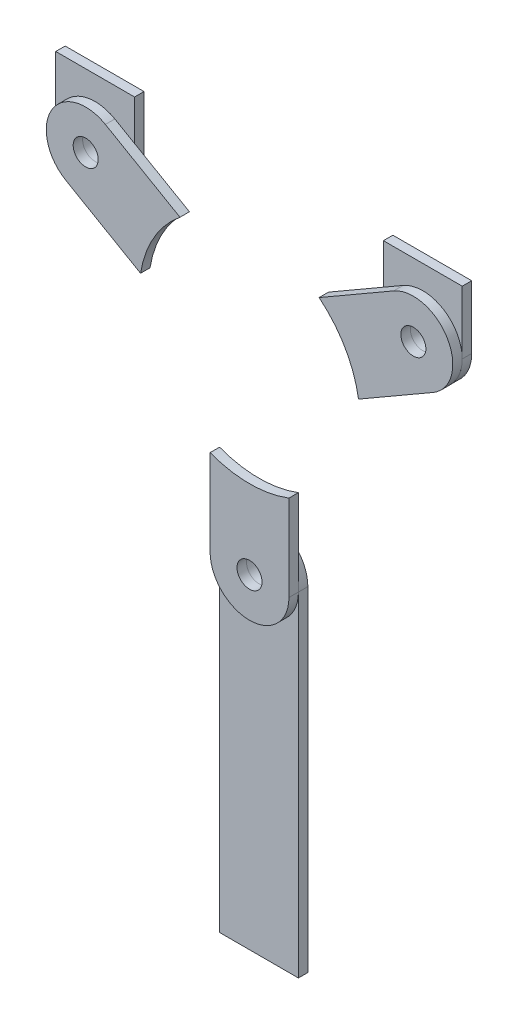
SolidWorks part; units mm, degrees
ref_plane "Front Plane" through (0, 0, 0) normal (0, 0, 1) x (1, 0, 0)
ref_plane "Top Plane" through (0, 0, 0) normal (0, 1, 0) x (1, 0, 0)
ref_plane "Right Plane" through (0, 0, 0) normal (1, 0, 0) x (0, 0, -1)
sketch "Sketch1" plane through (0, 0, 0) normal (0, 0, 1) x (1, 0, 0)
  line L0 (0, 60) -> (0, -60) construction
  line L1 (0, 0) -> (51.9615, 30) construction
  line L2 (0, 0) -> (-51.9615, 30) construction
  line L3 (45.7115, 40.8253) -> (22.0619, 27.1712)
  line L4 (58.2115, 19.1747) -> (34.5619, 5.5206)
  line L5 (12.5, -60) -> (12.5, -32.6917)
  line L6 (-12.5, -60) -> (-12.5, -32.6917)
  line L7 (-58.2115, 19.1747) -> (-34.5619, 5.5206)
  line L8 (-45.7115, 40.8253) -> (-22.0619, 27.1712)
  circle A0 centre (0, 0) radius 35 construction
  circle A1 centre (0, 0) radius 60 construction
  circle A2 centre (-51.9615, 30) radius 3.9687
  circle A3 centre (51.9615, 30) radius 3.9687
  circle A4 centre (0, -60) radius 3.9688
  arc A5 (45.7115, 40.8253) -> (58.2115, 19.1747) centre (51.9615, 30) cw
  arc A6 (22.0619, 27.1712) -> (34.5708, 5.4642) centre (0, 0) cw
  arc A7 (12.5, -60) -> (-12.5, -60) centre (0, -60) cw
  arc A8 (12.5, -32.6917) -> (-12.5533, -32.6713) centre (0, 0) cw
  arc A9 (-58.2115, 19.1747) -> (-45.7115, 40.8253) centre (-51.9615, 30) cw
  arc A10 (-34.5619, 5.5206) -> (-22.0175, 27.2071) centre (0, 0) cw
  point P31 (0, 0)
  dimension "D1" = 70
  dimension "D4" = 120
  dimension "D5" = 7.9375
  dimension "D6" = 3
  dimension "D7" = 12.5
  dimension "D2" = 60
  dimension "D3" = 60
extrude "Boss-Extrude1" add sketch "Sketch1" along normal blind 3 contours L7 A10 L8 A9 A2 | L3 A6 L4 A5 A3 | L5 A8 L6 A7 A4
sketch "Sketch2" plane through (0, 0, 0) normal (0, 0, 1) x (1, 0, 0)
  line L0 (-64.4615, 30) -> (-64.4615, 50)
  line L1 (-39.4615, 30) -> (-39.4615, 50)
  line L2 (-64.4615, 50) -> (-39.4615, 50)
  line L3 (0, 0) -> (0, 76.0953) construction
  line L4 (64.4615, 30) -> (64.4615, 50)
  line L5 (39.4615, 30) -> (39.4615, 50)
  line L6 (64.4615, 50) -> (39.4615, 50)
  line L7 (12.5, -60) -> (12.5, -32.6917) construction
  line L8 (-12.5, -60) -> (-12.5, -166)
  line L9 (-12.5, -166) -> (12.5, -166)
  line L10 (12.5, -166) -> (12.5, -60)
  circle A0 centre (51.9615, 30) radius 3.9688 construction
  circle A1 centre (-51.9615, 30) radius 3.9688 construction
  circle A2 centre (51.9615, 30) radius 3.9687
  circle A3 centre (-51.9615, 30) radius 3.9687
  arc A4 (-39.4615, 30) -> (-64.4615, 30) centre (-51.9615, 30) cw
  arc A5 (-45.7115, 40.8253) -> (-58.2115, 19.1747) centre (-51.9615, 30) ccw construction
  arc A6 (39.4615, 30) -> (64.4615, 30) centre (51.9615, 30) ccw
  arc A7 (-12.5, -60) -> (12.5, -60) centre (0, -60) cw
  circle A8 centre (0, -60) radius 3.9688 construction
  circle A9 centre (0, -60) radius 3.9688
  dimension "D1" = 20
  dimension "D2" = 106
extrude "Boss-Extrude2" add sketch "Sketch2" against normal blind 3 separate body
delete or keep bodies "Body-Delete1" [suppressed] type delete bodies bodies 101 102
delete or keep bodies "Body-Delete2" [suppressed] type delete bodies bodies 101 105 102 103 106
delete or keep bodies "Body-Delete3" [suppressed] type delete bodies bodies 104 105 102 101 103
